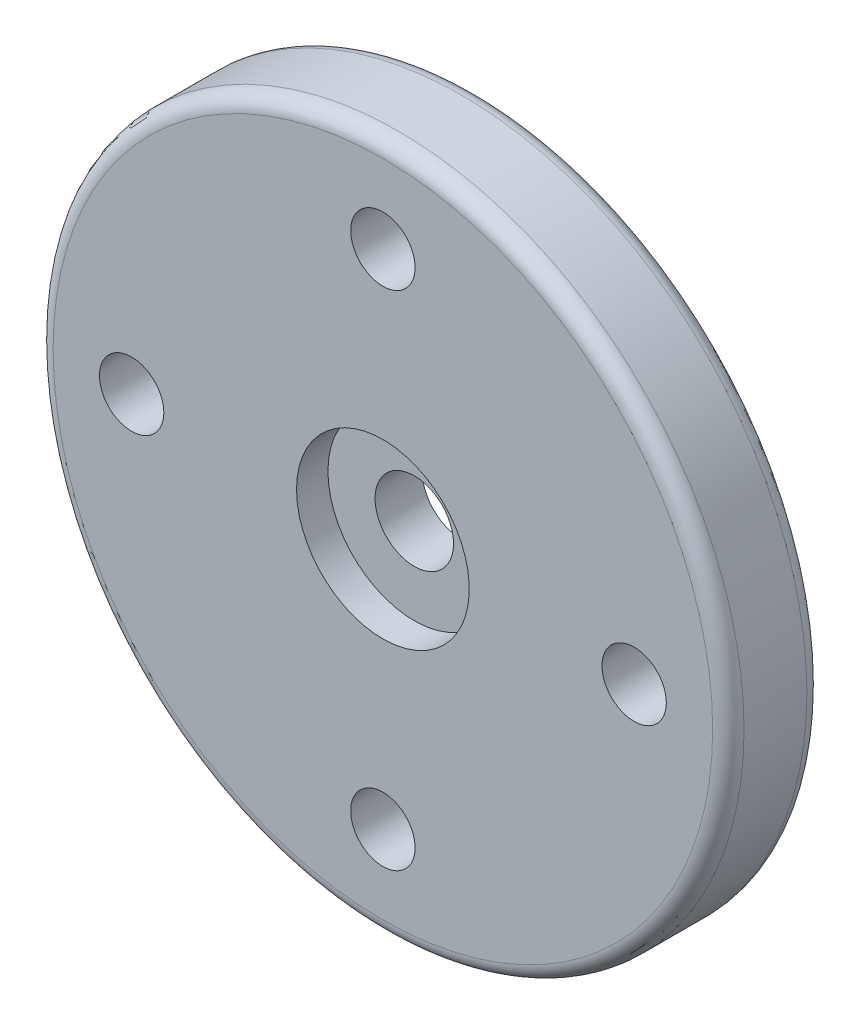
SolidWorks part; units mm, degrees
ref_plane "Front" through (0, 0, 0) normal (0, 0, 1) x (1, 0, 0)
ref_plane "Top" through (0, 0, 0) normal (0, 1, 0) x (1, 0, 0)
ref_plane "Right" through (0, 0, 0) normal (1, 0, 0) x (0, 0, -1)
sketch "Sketch1" plane through (0, 0, 0) normal (1, 0, 0) x (0, 0, -1)
  line L0 (0, 0) -> (-91.1734, 0) construction
  line L1 (2.5, 1.25) -> (1, 1.25)
  line L2 (0, 2.75) -> (0, 11)
  line L3 (0, 11) -> (3, 11)
  line L4 (3, 11) -> (3, 2.75)
  line L5 (3, 2.75) -> (2.5, 2.75)
  line L8 (2.5, 2.75) -> (2.5, 1.25)
  line L9 (0, 2.75) -> (1, 2.75)
  line L10 (1, 2.75) -> (1, 1.25)
  dimension "D1" = 2.5
  dimension "D2" = 5.5
  dimension "D3" = 1
  dimension "D4" = 3
  dimension "D5" = 22
  dimension "D6" = 1.5
revolve "Revolve1" add sketch "Sketch1" angle 360 about L0
hole_wizard "M2 Tapped Hole1" positions "Sketch3" profile "Sketch4" tap size "M2" standard "ISO" end condition up to next
sketch "Sketch3" plane through (0, 0, 0) normal (0, 0, 1) x (1, 0, 0)
  circle A0 centre (0, 0) radius 8 construction
  point P0 (0, 8)
  point P14 (8, 0)
  point P15 (0, -8)
  point P16 (-8, 0)
  point P17 (0, 0)
  dimension "D1" = 16
  dimension "D2" = 4
sketch "Sketch4" plane through (0, 8, 0) normal (1, 0, 0) x (0, -1, 0)
  line L0 (0, 0) -> (0, 3)
  line L1 (0, 3) -> (1.025, 3)
  line L2 (0.8, 2.8701) -> (0.8, 0.1299)
  line L3 (0.8, 0.1299) -> (1.025, 0)
  line L5 (1.025, 0) -> (0, 0)
  line L6 (-0.8, 0.1299) -> (-1.025, 0) construction
  line L7 (1.025, 3) -> (0.8, 2.8701)
  line L8 (-1.025, 3) -> (-0.8, 2.8701) construction
  line L11 (0, -6.35) -> (0, 107.95) construction
  dimension "Thru Tap Drill Dia." = 1.6
  dimension "Thru Tap Drill Depth" = 3
  dimension "Near C'Sink Dia." = 2.05
  dimension "Near C'Sink Angle" = 120
  dimension "Far C'Sink Dia." = 2.05
  dimension "Far C'Sink Angle" = 120
cosmetic thread "Hole Thread1" parameters "D2"=2
cosmetic thread "Hole Thread2" parameters "D2"=2
cosmetic thread "Hole Thread3" parameters "D2"=2
cosmetic thread "Hole Thread4" parameters "D2"=2
fillet "Radyus1" radius 0.5 2 edges at (-11, 0, -3) (-11, 0, 0)
sketch "Çizim1" plane through (0, 0, 0) normal (0, 0, 1) x (1, 0, 0)
  circle A0 centre (0, 8) radius 1.025
  circle A1 centre (-8, 0) radius 1.025
  circle A2 centre (8, 0) radius 1.025
  circle A3 centre (0, -8) radius 1.025
extrude "Kes-Ekstrüzyon1" cut sketch "Çizim1" against normal blind 10
